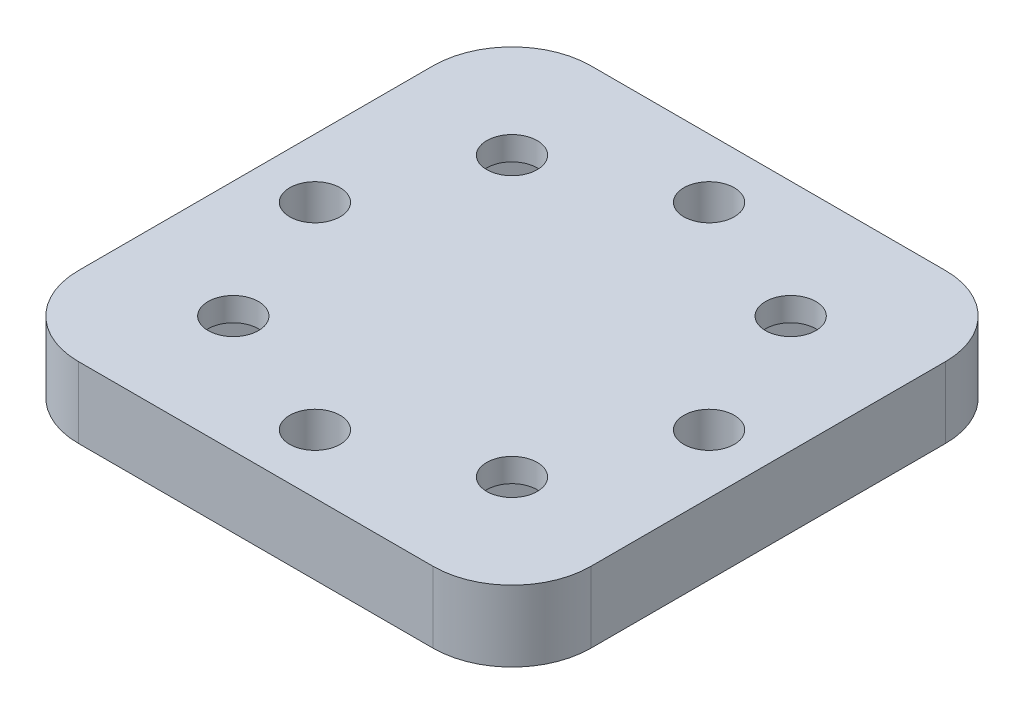
SolidWorks part; units mm, degrees
ref_plane "정면" through (0, 0, 0) normal (0, 0, 1) x (1, 0, 0)
ref_plane "윗면" through (0, 0, 0) normal (0, 1, 0) x (1, 0, 0)
ref_plane "우측면" through (0, 0, 0) normal (1, 0, 0) x (0, 0, -1)
sketch "스케치1" plane through (0, 0, 0) normal (0, 1, 0) x (1, 0, 0)
  line L1 (-32.5, 32.5) -> (32.5, 32.5)
  line L2 (-32.5, 32.5) -> (-32.5, -32.5)
  line L3 (-32.5, -32.5) -> (32.5, -32.5)
  line L4 (32.5, 32.5) -> (32.5, -32.5)
  point P4 (32.5, 0)
  point P6 (0, 32.5)
  dimension "D1" = 65
  dimension "D2" = 65
extrude "보스-돌출1" add sketch "스케치1" along normal blind 9
sketch "스케치2" plane through (0, 9, 0) normal (0, 1, 0) x (1, 0, 0)
  line L0 (17.6777, 17.6777) -> (-17.6777, -17.6777) construction
  line L1 (-17.6777, 17.6777) -> (17.6777, -17.6777) construction
  line L2 (0, 25) -> (0, -25) construction
  line L3 (25, 0) -> (-25, 0) construction
  circle A0 centre (-17.6777, 17.6777) radius 3.2
  circle A1 centre (17.6777, -17.6777) radius 3.2
  circle A2 centre (-17.6777, -17.6777) radius 3.2
  circle A3 centre (17.6777, 17.6777) radius 3.2
  circle A4 centre (0, 25) radius 3.2
  circle A5 centre (25, 0) radius 3.2
  circle A6 centre (0, -25) radius 3.2
  circle A7 centre (-25, 0) radius 3.2
  point P14 (0, 0)
  point P15 (0, 0)
  point P18 (0, 0)
  point P19 (0, 0)
  point P20 (17.6134, -17.7417)
  dimension "D4" = 6.4
  dimension "D1" = 90
  dimension "D2" = 45
  dimension "D3" = 50
extrude "컷-돌출1" cut sketch "스케치2" against normal up to surface (9 mm away) up to face at (0, 0, 0)
sketch "스케치3" plane through (0, 0, 0) normal (0, -1, 0) x (1, 0, 0)
  line L0 (-25.0316, 17.6777) -> (-17.6777, 10.3238)
  line L1 (-25.0316, 17.6777) -> (-17.6777, 25.0316)
  line L2 (-17.6777, 10.3238) -> (-10.3238, 17.6777)
  line L3 (-17.6777, 25.0316) -> (-10.3238, 17.6777)
  line L4 (10.3238, 17.6777) -> (17.6777, 10.3238)
  line L5 (10.3238, 17.6777) -> (17.6777, 25.0316)
  line L6 (17.6777, 10.3238) -> (25.0316, 17.6777)
  line L7 (17.6777, 25.0316) -> (25.0316, 17.6777)
  line L8 (10.3238, -17.6777) -> (17.6777, -25.0316)
  line L9 (10.3238, -17.6777) -> (17.6777, -10.3238)
  line L10 (17.6777, -25.0316) -> (25.0316, -17.6777)
  line L11 (17.6777, -10.3238) -> (25.0316, -17.6777)
  line L12 (-25.0316, -17.6777) -> (-17.6777, -25.0316)
  line L13 (-25.0316, -17.6777) -> (-17.6777, -10.3238)
  line L14 (-17.6777, -25.0316) -> (-10.3238, -17.6777)
  line L15 (-17.6777, -10.3238) -> (-10.3238, -17.6777)
  line L16 (-17.6777, 17.6777) -> (17.6777, -17.6777) construction
  line L17 (17.6777, 17.6777) -> (-17.6777, -17.6777) construction
  line L18 (17.6777, 25.0316) -> (17.6777, 10.3238) construction
  line L19 (10.3238, 17.6777) -> (25.0316, 17.6777) construction
  line L20 (17.6777, -10.3238) -> (17.6777, -25.0316) construction
  line L22 (10.3238, -17.6777) -> (25.0316, -17.6777) construction
  line L23 (-17.6777, -10.3238) -> (-17.6777, -25.0316) construction
  line L24 (-10.3238, -17.6777) -> (-25.0316, -17.6777) construction
  line L25 (-17.6777, 25.0316) -> (-17.6777, 10.3238) construction
  line L26 (-25.0316, 17.6777) -> (-10.3238, 17.6777) construction
  point P14 (17.6777, -25.0316)
  point P24 (-14.0007, 14.0007)
  point P25 (14.0007, -14.0007)
  point P26 (-14.0007, -14.0007)
  point P27 (14.0007, 14.0007)
  point P28 (17.6777, 17.6777)
  point P29 (17.6777, -17.6777)
  point P31 (-17.6777, -17.6777)
  point P32 (-17.6777, 17.6777)
  point P34 (0, 0)
  point P35 (0, 0)
  point P36 (0, 0)
  point P37 (17.3174, -25.2501)
  dimension "D1" = 10.4
extrude "컷-돌출2" cut sketch "스케치3" against normal offset from surface (6 mm away) 3 up to face at (0, 9, 28.2)
fillet "필렛1" radius 10 4 edges at (32.5, 4.5, 32.5) (-32.5, 4.5, 32.5) (-32.5, 4.5, -32.5) (32.5, 4.5, -32.5)
